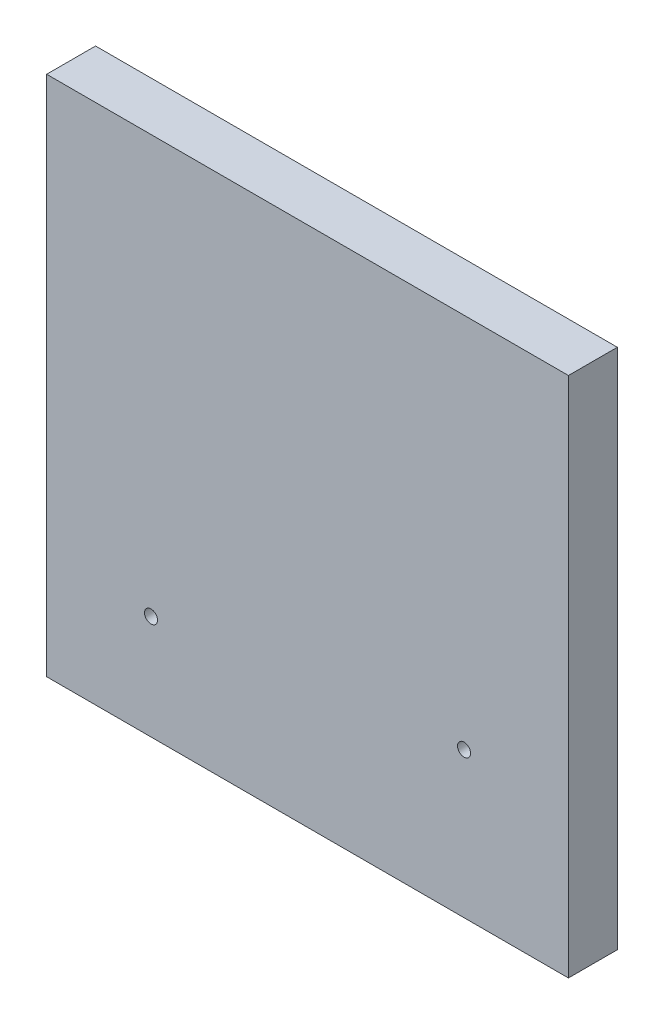
SolidWorks part; units mm, degrees
material "Pine"
ref_plane "Front Plane" through (0, 0, 0) normal (0, 0, 1) x (1, 0, 0)
ref_plane "Top Plane" through (0, 0, 0) normal (0, 1, 0) x (1, 0, 0)
ref_plane "Right Plane" through (0, 0, 0) normal (1, 0, 0) x (0, 0, -1)
sketch "Sketch1" plane through (0, 0, 0) normal (0, 0, 1) x (1, 0, 0)
  line L1 (0, 0) -> (127, 0)
  line L2 (0, 0) -> (0, 127)
  line L3 (0, 127) -> (127, 127)
  line L4 (127, 0) -> (127, 127)
  circle A0 centre (25.4, 25.4) radius 1.5875
  circle A1 centre (101.6, 35.433) radius 1.5875
  dimension "D3" = 3.175
  dimension "D1" = 127
  dimension "D2" = 127
  dimension "D4" = 76.2
  dimension "D5" = 25.4
  dimension "D6" = 25.4
  dimension "D7" = 10.033
extrude "Boss-Extrude1" add sketch "Sketch1" along normal blind 11.9062
